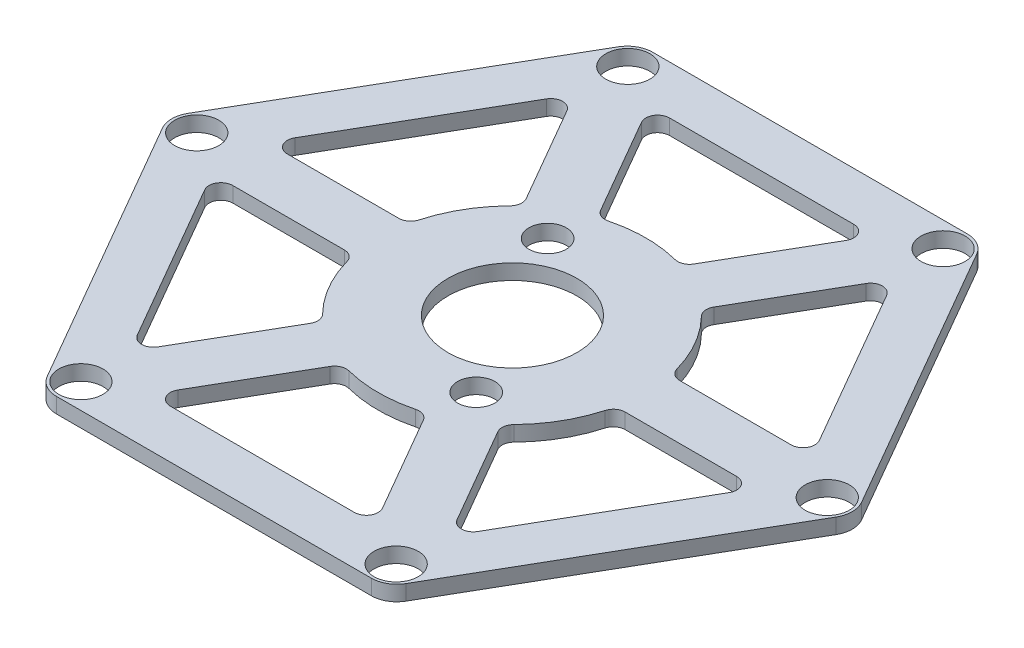
SolidWorks part; units mm, degrees
ref_plane "Front Plane" through (0, 0, 0) normal (0, 0, 1) x (1, 0, 0)
ref_plane "Top Plane" through (0, 0, 0) normal (0, 1, 0) x (1, 0, 0)
ref_plane "Right Plane" through (0, 0, 0) normal (1, 0, 0) x (0, 0, -1)
sketch "Sketch1" plane through (0, 0, 0) normal (0, 1, 0) x (1, 0, 0)
  line L1 (-20.3, 35.1606) -> (-40.6, 0)
  line L2 (-40.6, 0) -> (-20.3, -35.1606)
  line L3 (-20.3, -35.1606) -> (20.3, -35.1606)
  line L4 (20.3, -35.1606) -> (40.6, 0)
  line L5 (40.6, 0) -> (20.3, 35.1606)
  line L6 (20.3, 35.1606) -> (-20.3, 35.1606)
  line L7 (-17, 29.4449) -> (-34, 0)
  line L8 (-34, 0) -> (-17, -29.4449)
  line L9 (-17, -29.4449) -> (17, -29.4449)
  line L10 (17, -29.4449) -> (34, 0)
  line L11 (34, 0) -> (17, 29.4449)
  line L12 (17, 29.4449) -> (-17, 29.4449)
  line L13 (-18.6638, 32.2165) -> (-37.3656, -0.0563) construction
  line L14 (-37.3656, -0.0563) -> (-18.7674, -32.3889) construction
  line L15 (-18.7674, -32.3889) -> (18.5325, -32.4487) construction
  line L16 (18.5325, -32.4487) -> (37.3, 0) construction
  line L17 (37.3, 0) -> (18.6362, 32.2165) construction
  line L18 (18.6362, 32.2165) -> (-18.6638, 32.2165) construction
  line L50 (-17, 29.4449) -> (17, -29.4449) construction
  line L51 (-17, 29.4449) -> (-18.8579, 26.2268)
  line L56 (-13.2841, 29.4449) -> (-17, 29.4449)
  line L57 (-13.3543, 16.6943) -> (-7.7805, 19.9123) construction
  line L58 (-17, 29.4449) -> (-13.2841, 29.4449)
  line L59 (-13.2841, 29.4449) -> (-4.9475, 15.0054)
  line L60 (-17, 29.4449) -> (-18.8579, 26.2268)
  line L61 (-18.8579, 26.2268) -> (-10.5213, 11.7874)
  line L62 (17, 29.4449) -> (13.2841, 29.4449)
  line L63 (13.2841, 29.4449) -> (4.9475, 15.0054)
  line L66 (18.8579, 26.2268) -> (10.5213, 11.7874)
  line L67 (17, 29.4449) -> (18.8579, 26.2268)
  line L68 (34, 0) -> (32.1421, 3.2181)
  line L69 (32.1421, 3.2181) -> (15.4688, 3.2181)
  line L72 (32.1421, -3.2181) -> (15.4688, -3.2181)
  line L73 (34, 0) -> (32.1421, -3.2181)
  line L74 (17, -29.4449) -> (18.8579, -26.2268)
  line L75 (18.8579, -26.2268) -> (10.5213, -11.7874)
  line L78 (13.2841, -29.4449) -> (4.9475, -15.0054)
  line L79 (17, -29.4449) -> (13.2841, -29.4449)
  line L80 (-17, -29.4449) -> (-13.2841, -29.4449)
  line L81 (-13.2841, -29.4449) -> (-4.9475, -15.0054)
  line L84 (-18.8579, -26.2268) -> (-10.5213, -11.7874)
  line L85 (-17, -29.4449) -> (-18.8579, -26.2268)
  line L86 (-34, 0) -> (-32.1421, -3.2181)
  line L87 (-32.1421, -3.2181) -> (-15.4688, -3.2181)
  line L90 (-32.1421, 3.2181) -> (-15.4688, 3.2181)
  line L91 (-34, 0) -> (-32.1421, 3.2181)
  line L92 (18.6362, 32.2165) -> (31.4889, 27.5601) construction
  circle A0 centre (0.0529, 0) radius 7.6
  circle A2 centre (0.0529, 0) radius 11.5 construction
  circle A3 centre (-5.7367, 9.9363) radius 2.2
  arc A4 (-10.5213, 11.7874) -> (-15.4688, 3.2181) centre (0, 0) ccw
  arc A5 (4.9475, 15.0054) -> (-4.9475, 15.0054) centre (0, 0) ccw
  arc A6 (15.4688, 3.2181) -> (10.5213, 11.7874) centre (0, 0) ccw
  arc A7 (10.5213, -11.7874) -> (15.4688, -3.2181) centre (0, 0) ccw
  arc A8 (-4.9475, -15.0054) -> (4.9475, -15.0054) centre (0, 0) ccw
  arc A9 (-15.4688, -3.2181) -> (-10.5213, -11.7874) centre (0, 0) ccw
  circle A10 centre (5.7632, -9.9821) radius 2.2
  circle A16 centre (18.6362, 32.2165) radius 2.6
  circle A17 centre (37.2184, -0.0312) radius 2.6
  circle A18 centre (18.5822, -32.2477) radius 2.6
  circle A19 centre (-18.6362, -32.2165) radius 2.6
  circle A20 centre (-37.2184, 0.0312) radius 2.6
  circle A21 centre (-18.5822, 32.2477) radius 2.6
  point P40 (0, 0)
  point P42 (0, 0)
  point P58 (0.0529, 0)
  point P59 (0, 0)
  point P62 (0, 0)
  point P77 (0, 0)
  point P82 (0, 0)
  point P92 (0, 0)
  dimension "D7" = 6
  dimension "D5" = 40
  dimension "D6" = 5.2
  dimension "D1" = 40.6
  dimension "D2" = 6.6
  dimension "D3" = 3.3
  dimension "D4" = 6
extrude "Boss-Extrude1" add sketch "Sketch1" along normal blind 1.8
fillet "Fillet1" radius 3 6 edges at (-40.6, 0.9, 0) (-20.3, 0.9, 35.1606) (20.3, 0.9, 35.1606) (40.6, 0.9, 0) (20.3, 0.9, -35.1606) (-20.3, 0.9, -35.1606)
fillet "Fillet2" radius 1.4 24 edges at (-32.1421, 0.9, 3.2181) (-15.4688, 0.9, 3.2181) (-10.5213, 0.9, 11.7874) (-18.8579, 0.9, 26.2268) (-13.2841, 0.9, 29.4449) (13.2841, 0.9, 29.4449) (-4.9475, 0.9, 15.0054) (4.9475, 0.9, 15.0054) (18.8579, 0.9, 26.2268) (10.5213, 0.9, 11.7874) (15.4688, 0.9, 3.2181) (32.1421, 0.9, 3.2181) (32.1421, 0.9, -3.2181) (18.8579, 0.9, -26.2268) (15.4688, 0.9, -3.2181) (10.5213, 0.9, -11.7874) (-32.1421, 0.9, -3.2181) (-15.4688, 0.9, -3.2181) (-4.9475, 0.9, -15.0054) (-13.2841, 0.9, -29.4449) (4.9475, 0.9, -15.0054) (13.2841, 0.9, -29.4449) (-10.5213, 0.9, -11.7874) (-18.8579, 0.9, -26.2268)
ref_plane "Plane1" through (0, 1.8, 0) normal (0, 1, 0) x (1, 0, 0)
scale "Scale1" scale about centroid uniform scaling yes scale factor 1.15
